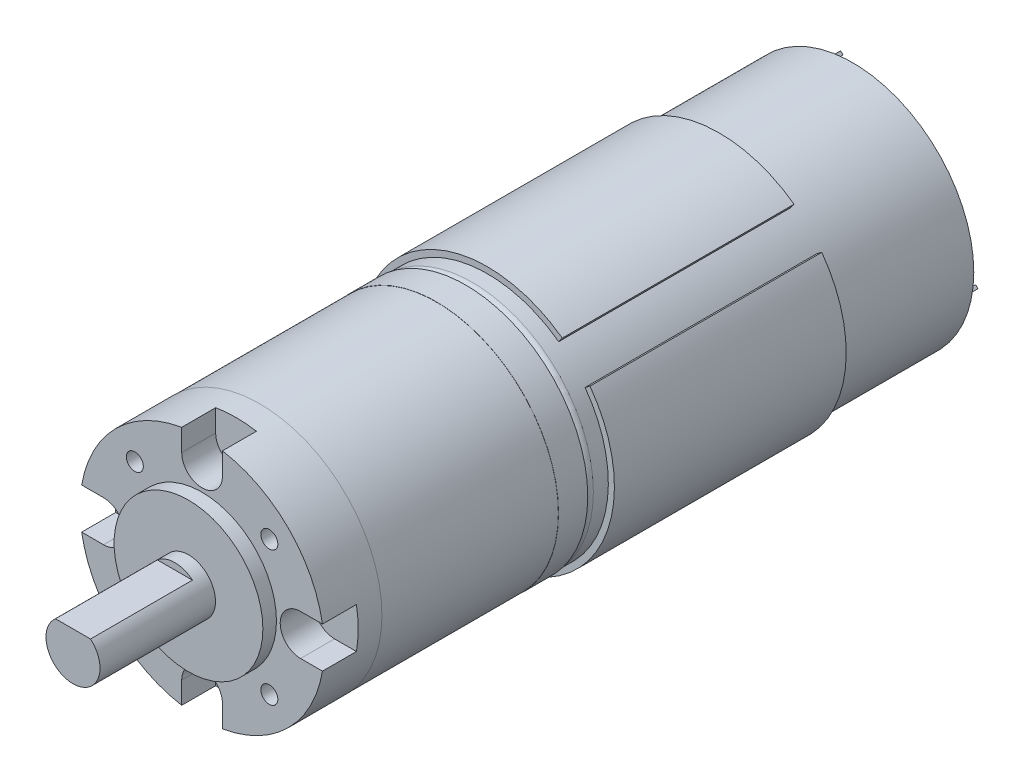
SolidWorks part; units mm, degrees
material "AISI 1045 Steel, cold drawn"
ref_plane "Front Plane" through (0, 0, 0) normal (0, 0, 1) x (1, 0, 0)
ref_plane "Top Plane" through (0, 0, 0) normal (0, 1, 0) x (1, 0, 0)
ref_plane "Right Plane" through (0, 0, 0) normal (1, 0, 0) x (0, 0, -1)
sketch "Sketch1" plane through (0, 0, 0) normal (0, 0, 1) x (1, 0, 0)
  circle A0 centre (0, 0) radius 17.975
  dimension "D1" = 35.95
extrude "Boss-Extrude1" add sketch "Sketch1" along normal blind 8.5
sketch "Sketch2" plane through (0, 0, 8.5) normal (0, 0, 1) x (1, 0, 0)
  line L0 (0, 0) -> (-14.5, 0) construction
  line L1 (0, 0) -> (0, 14.5) construction
  line L2 (-14.5, 0) -> (-24.5, 0) construction
  line L3 (-14.5, -3) -> (-24.5, -3)
  line L4 (-14.5, 3) -> (-24.5, 3)
  line L5 (14.5, 0) -> (24.5, 0) construction
  line L6 (14.5, -3) -> (24.5, -3)
  line L7 (14.5, 3) -> (24.5, 3)
  line L8 (0, 14.5) -> (0, 24.5) construction
  line L9 (-3, 14.5) -> (-3, 24.5)
  line L10 (3, 14.5) -> (3, 24.5)
  line L11 (0, -14.5) -> (0, -24.5) construction
  line L12 (-3, -14.5) -> (-3, -24.5)
  line L13 (3, -14.5) -> (3, -24.5)
  arc A0 (-14.5, -3) -> (-14.5, 3) centre (-14.5, 0) ccw
  arc A1 (-24.5, 3) -> (-24.5, -3) centre (-24.5, 0) ccw
  arc A2 (14.5, -3) -> (14.5, 3) centre (14.5, 0) cw
  arc A3 (24.5, 3) -> (24.5, -3) centre (24.5, 0) cw
  arc A4 (-3, 14.5) -> (3, 14.5) centre (0, 14.5) ccw
  arc A5 (3, 24.5) -> (-3, 24.5) centre (0, 24.5) ccw
  arc A6 (-3, -14.5) -> (3, -14.5) centre (0, -14.5) cw
  arc A7 (3, -24.5) -> (-3, -24.5) centre (0, -24.5) cw
  point P5 (-19.5, 0)
  point P12 (19.5, 0)
  point P18 (0, 19.5)
  point P25 (0, -19.5)
  point P30 (-11.5, 0)
  point P31 (11.5, 0)
  dimension "D1" = 6
  dimension "D2" = 23
  dimension "D3" = 10
extrude "Cut-Extrude1" cut sketch "Sketch2" against normal blind 5
sketch "Sketch3" plane through (0, 0, 8.5) normal (0, 0, 1) x (1, 0, 0)
  circle A0 centre (0, 0) radius 10.95
  dimension "D1" = 21.9
extrude "Boss-Extrude2" add sketch "Sketch3" along normal blind 2
sketch "Sketch4" plane through (0, 0, 10.5) normal (0, 0, 1) x (1, 0, 0)
  circle A0 centre (0, 0) radius 3.975
  dimension "D1" = 7.95
extrude "Boss-Extrude3" add sketch "Sketch4" along normal blind 17 separate body
sketch "Sketch5" plane through (0, 0, 27.5) normal (0, 0, 1) x (1, 0, 0)
  line L0 (0, 3.025) -> (0, -3.975) construction
  line L1 (2.5788, 3.975) -> (-2.5788, 3.975)
  line L2 (2.5788, 3.975) -> (2.5788, 3.025)
  line L3 (2.5788, 3.025) -> (-2.5788, 3.025)
  line L4 (-2.5788, 3.975) -> (-2.5788, 3.025)
  circle A0 centre (0, 0) radius 3.975 construction
  dimension "D1" = 7
extrude "Cut-Extrude2" cut sketch "Sketch5" against normal blind 15
sketch "Sketch6" plane through (0, 0, 8.5) normal (0, 0, 1) x (1, 0, 0)
  line L0 (0, 0) -> (-9.8995, 9.8995) construction
  line L1 (0, 0) -> (9.8995, 9.8995) construction
  line L2 (0, 0) -> (-9.8995, -9.8995) construction
  line L3 (0, 0) -> (9.8995, -9.8995) construction
  line L4 (-17.7229, -3) -> (-14.5, -3) construction
  circle A0 centre (0, 0) radius 14 construction
  dimension "D1" = 28
  dimension "D2" = 90
  dimension "D3" = 45
hole_wizard "M3x0.5 Tapped Hole1" positions "3DSketch2" profile "Sketch7" tap size "M3x0.5" standard "ANSI Metric" end condition through all
sketch3d "3DSketch2"
  circle A0 centre (0, 0, 8.5) radius 14 construction
  point P0 (-9.8995, 9.8995, 8.5)
  point P4 (0, 0, 22.5)
  point P5 (-9.8995, -9.8995, 8.5)
  point P8 (9.8995, -9.8995, 8.5)
  point P11 (9.8995, 9.8995, 8.5)
cosmetic thread "Hole Thread1" parameters "D2"=3
cosmetic thread "Hole Thread2" parameters "D2"=3
cosmetic thread "Hole Thread3" parameters "D2"=3
cosmetic thread "Hole Thread4" parameters "D2"=3
sketch "Sketch7" plane through (-9.8995, 9.8995, 8.5) normal (1, 0, 0) x (0, -1, 0)
  line L0 (0, 0) -> (0, 8.5)
  line L1 (0, 8.5) -> (1.25, 8.5)
  line L2 (1.25, 8.5) -> (1.25, 0)
  line L5 (1.25, 0) -> (0, 0)
  line L11 (0, -6.35) -> (0, 107.95) construction
  dimension "Thru Tap Drill Dia." = 2.5
  dimension "Thru Tap Drill Depth" = 8.5
sketch "Sketch8" plane through (0, 0, 0) normal (0, 0, -1) x (-1, 0, 0)
  circle A0 centre (0, 0) radius 17.95
  dimension "D1" = 35.9
extrude "Boss-Extrude4" add sketch "Sketch8" along normal blind 26 separate body
sketch "Sketch9" plane through (0, 0, -26) normal (0, 0, -1) x (-1, 0, 0)
  circle A0 centre (0, 0) radius 17.975 construction
  circle A1 centre (0, 0) radius 17.975
  dimension "D1" = 35.95
extrude "Boss-Extrude5" add sketch "Sketch9" along normal blind 4.3 separate body
sketch "Sketch10" plane through (0, 0, -30.3) normal (0, 0, -1) x (-1, 0, 0)
  circle A0 centre (0, 0) radius 17.8
  dimension "D1" = 35.6
extrude "Boss-Extrude6" add sketch "Sketch10" along normal blind 57 separate body
fillet "Fillet1" radius 1 1 edges at (-17.8, 0, -30.3)
ref_plane "Plane1" through (0, 0, -90.25) normal (0, 0, 1) x (1, 0, 0)
sketch "Sketch11" plane through (0, 0, -90.25) normal (0, 0, 1) x (1, 0, 0)
  circle A0 centre (0, 0) radius 5.375
  dimension "D1" = 10.75
extrude "Boss-Extrude7" add sketch "Sketch11" along normal up to surface (2.95 mm away) up to face at (-17.8, 0, -87.3)
sketch "Sketch12" plane through (0, 0, -87.3) normal (0, 0, -1) x (-1, 0, 0)
  line L0 (0, 0) -> (-10.5593, 0) construction
  line L1 (0, 0) -> (-6.7751, 6.7751) construction
  line L2 (0, 0) -> (9.9349, 9.9349) construction
  line L3 (8.4499, 11.0662) -> (11.0662, 8.4499)
  line L4 (8.4499, 11.0662) -> (8.8035, 11.4198)
  line L5 (11.0662, 8.4499) -> (11.4198, 8.8035)
  line L6 (8.8035, 11.4198) -> (11.4198, 8.8035)
  line L7 (8.4499, 11.0662) -> (11.4198, 8.8035) construction
  line L8 (11.0662, 8.4499) -> (8.8035, 11.4198) construction
  line L9 (-8.4499, -11.0662) -> (-11.4198, -8.8035) construction
  line L10 (-11.0662, -8.4499) -> (-8.8035, -11.4198) construction
  line L11 (-11.4198, -8.8035) -> (-8.8035, -11.4198)
  line L12 (-8.4499, -11.0662) -> (-8.8035, -11.4198)
  line L13 (-11.0662, -8.4499) -> (-11.4198, -8.8035)
  line L14 (-11.0662, -8.4499) -> (-8.4499, -11.0662)
  dimension "D1" = 3.7
  dimension "D2" = 0.5
  dimension "D3" = 45
  dimension "D4" = 28.6
extrude "Boss-Extrude8" add sketch "Sketch12" along normal blind 7 separate body
ref_plane "Plane2" through (0, 0, -33.5) normal (0, 0, 1) x (1, 0, 0)
ref_plane "Plane3" through (0, 0, -67.62) normal (0, 0, 1) x (1, 0, 0)
sketch "Sketch13" plane through (0, 0, -33.5) normal (0, 0, 1) x (1, 0, 0)
  line L0 (0, 0) -> (6.796, 0) construction
  line L1 (0, 0) -> (15.1366, 15.1366) construction
  line L2 (10.4908, 14.3799) -> (11.0213, 15.107)
  line L3 (14.3799, 10.4908) -> (15.107, 11.0213)
  circle A0 centre (0, 0) radius 17.8
  circle A1 centre (0, 0) radius 17.8 construction
  arc A2 (10.4908, 14.3799) -> (14.3799, 10.4908) centre (0, 0) ccw
  arc A3 (11.0213, 15.107) -> (15.107, 11.0213) centre (0, 0) ccw
  dimension "D1" = 45
  dimension "D2" = 5.5
  dimension "D4" = 0.9
  dimension "D3" = 0.9
extrude "Boss-Extrude9" add sketch "Sketch13" against normal up to surface (34.12 mm away) separate body up to plane "Plane3"
sketch "Croquis1" plane through (0, 0, 0) normal (0, 1, 0) x (1, 0, 0)
  line L0 (0, 90.25) -> (0, -27.5) construction
  line L1 (5.375, 90.25) -> (-5.375, 90.25) construction
  line L2 (-2.5788, -27.5) -> (2.5788, -27.5) construction
  dimension "D1" = 117.75
sketch "Croquis2" plane through (0, 0, 8.5) normal (0, 0, 1) x (1, 0, 0)
  circle A0 centre (0, 0) radius 17.975
  circle A1 centre (0, 0) radius 18.7
  dimension "D1" = 35.95
  dimension "D2" = 37.4
